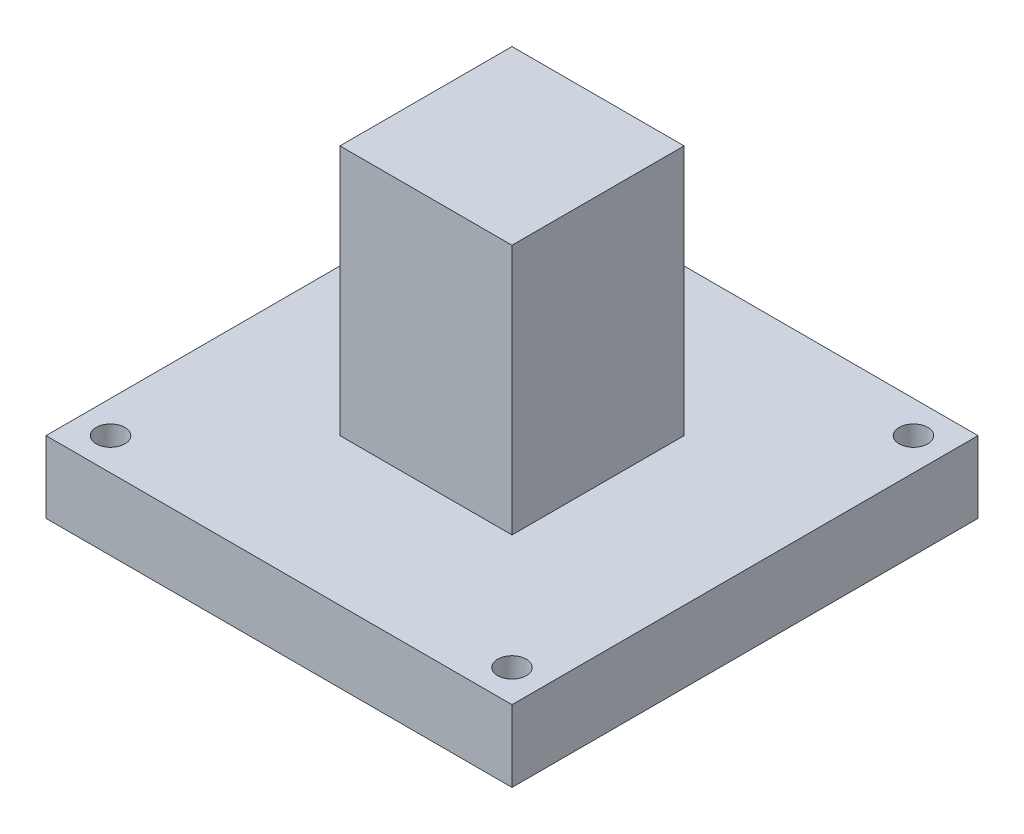
SolidWorks part; units mm, degrees
ref_plane "Front Plane" through (0, 0, 0) normal (0, 0, 1) x (1, 0, 0)
ref_plane "Top Plane" through (0, 0, 0) normal (0, 1, 0) x (1, 0, 0)
ref_plane "Right Plane" through (0, 0, 0) normal (1, 0, 0) x (0, 0, -1)
sketch "Sketch1" plane through (0, 0, 0) normal (0, 1, 0) x (1, 0, 0)
  line L1 (0, 0) -> (24, 0)
  line L2 (0, 0) -> (0, 24)
  line L3 (0, 24) -> (24, 24)
  line L4 (24, 0) -> (24, 24)
  dimension "D1" = 24
  dimension "D2" = 24
extrude "Boss-Extrude1" add sketch "Sketch1" along normal blind 35
sketch "Sketch2" plane through (0, 0, 0) normal (0, -1, 0) x (1, 0, 0)
  line L0 (0, -24) -> (0, 0) construction
  line L1 (44.5, 20.5) -> (-20.5, 20.5)
  line L2 (44.5, 20.5) -> (44.5, -44.5)
  line L3 (44.5, -44.5) -> (-20.5, -44.5)
  line L4 (-20.5, 20.5) -> (-20.5, -44.5)
  line L5 (0, 0) -> (24, 0) construction
  circle A0 centre (-16, 16) radius 2
  circle A1 centre (-16, -40) radius 2
  circle A2 centre (40, 16) radius 2
  circle A3 centre (40, -40) radius 2
  point P4 (-20.5, -12)
  point P7 (0, -12)
  point P8 (12, 20.5)
  point P11 (12, 0)
  dimension "D5" = 4
  dimension "D10" = 4
  dimension "D11" = 4
  dimension "D13" = 4
  dimension "D1" = 65
  dimension "D2" = 65
  dimension "D3" = 0
  dimension "D4" = 0
  dimension "D6" = 4.5
  dimension "D7" = 4.5
  dimension "D8" = 4.5
  dimension "D9" = 4.5
  dimension "D12" = 4.5
extrude "Boss-Extrude2" add sketch "Sketch2" along normal blind 10
sketch "Sketch3" plane through (0, -10, 0) normal (0, -1, 0) x (1, 0, 0)
  line L0 (44.5, 20.5) -> (-20.5, 20.5) construction
  line L1 (-20.5, -44.5) -> (44.5, -44.5) construction
  circle A0 centre (12, 16) radius 2.5
  circle A1 centre (12, -40) radius 2.5
  dimension "D1" = 5
  dimension "D3" = 5
  dimension "D2" = 4.5
  dimension "D4" = 4.5
extrude "Cut-Extrude1" cut sketch "Sketch3" against normal blind 7
